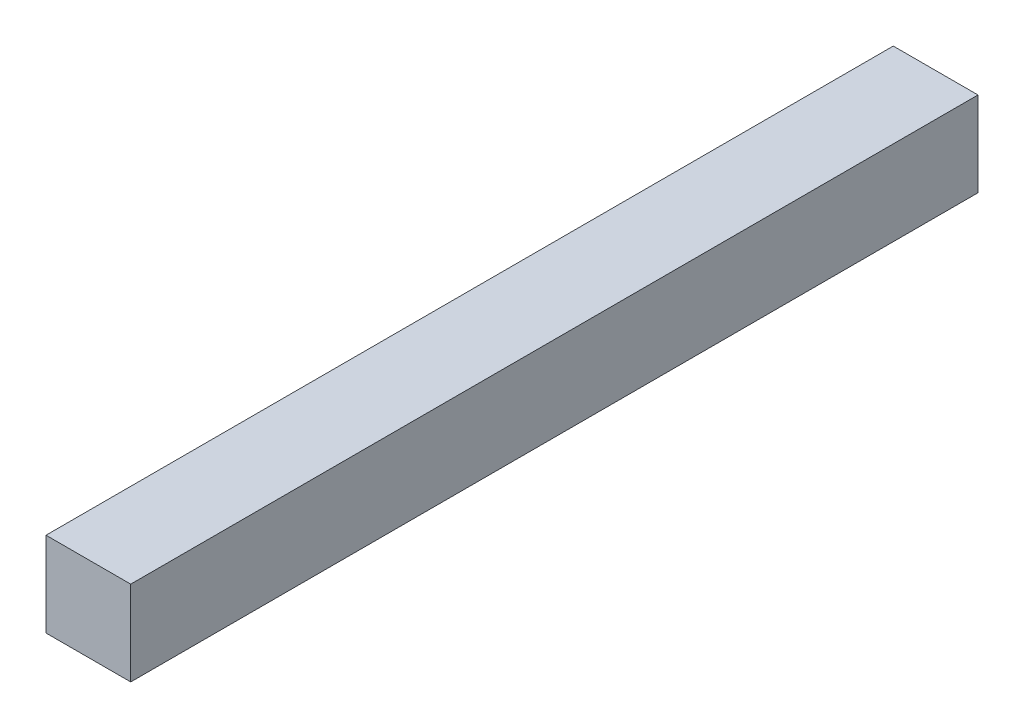
SolidWorks part; units mm, degrees
ref_plane "Front Plane" through (0, 0, 0) normal (0, 0, 1) x (1, 0, 0)
ref_plane "Top Plane" through (0, 0, 0) normal (0, 1, 0) x (1, 0, 0)
ref_plane "Right Plane" through (0, 0, 0) normal (1, 0, 0) x (0, 0, -1)
sketch "Sketch1" plane through (0, 0, 0) normal (0, 0, 1) x (1, 0, 0)
  line L1 (0, 0) -> (5, 0)
  line L2 (0, 0) -> (0, 5)
  line L3 (0, 5) -> (5, 5)
  line L4 (5, 0) -> (5, 5)
extrude "Boss-Extrude1" add sketch "Sketch1" along normal blind 50
